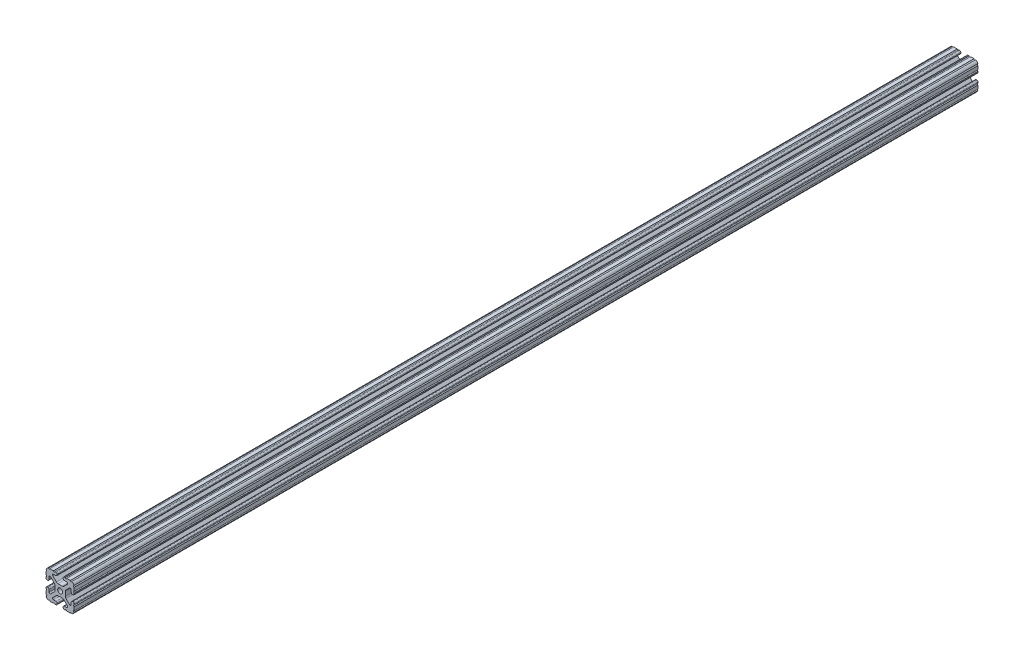
SolidWorks part; units mm, degrees
ref_plane "Front Plane" through (0, 0, 0) normal (0, 0, 1) x (1, 0, 0)
ref_plane "Top Plane" through (0, 0, 0) normal (0, 1, 0) x (1, 0, 0)
ref_plane "Right Plane" through (0, 0, 0) normal (1, 0, 0) x (0, 0, -1)
sketch "Sketch2" plane through (0, 0, 0) normal (0, 0, 1) x (1, 0, 0)
  line L0 (0, 19.05) -> (0, -19.05) construction
  line L1 (-19.05, 0) -> (19.05, 0) construction
  line L2 (4.064, -19.05) -> (19.05, -19.05)
  line L3 (19.05, -19.05) -> (19.05, -4.064)
  line L4 (4.064, -19.05) -> (4.064, -14.986)
  line L5 (4.064, -14.986) -> (12.1123, -14.986)
  line L6 (12.1123, -14.986) -> (4.1113, -6.985)
  line L7 (0, 0) -> (19.05, -19.05) construction
  line L8 (19.05, -4.064) -> (14.986, -4.064)
  line L9 (14.986, -4.064) -> (14.986, -12.1123)
  line L10 (14.986, -12.1123) -> (6.985, -4.1113)
  circle A0 centre (0, 0) radius 3.3274
  arc A1 (8.9963, -14.986) -> (9.909, -12.7826) centre (8.9963, -13.6953) ccw construction
  point P8 (0, -6.985)
  dimension "Center Hole Diameter" = 6.6548
  dimension "Rail Height" = 38.1
  dimension "Rail Width" = 38.1
  dimension "T-Slot Width" = 8.128
  dimension "Slot Inner Width" = 20.574
  dimension "Thickness" = 4.064
  dimension "Slot Depth" = 8.001
  dimension "D1" = 4.064
sketch "Sketch3" plane through (0, 0, 0) normal (1, 0, 0) x (0, 0, -1)
  line L0 (-609.6, -19.05) -> (609.6, -19.05) construction
  line L1 (-584.2, 0) -> (584.2, 0) construction
  dimension "Length" = 1219.2
  dimension "D1" = 25.4
sketch "Sketch4" plane through (0, 0, 0) normal (0, 0, 1) x (1, 0, 0)
  line L0 (5.7912, -19.05) -> (14.3002, -19.05)
  line L1 (4.064, -19.05) -> (19.05, -19.05) construction
  line L2 (4.064, -19.05) -> (4.064, -14.986) construction
  line L3 (4.064, -14.986) -> (12.1123, -14.986) construction
  line L4 (4.064, -16.7132) -> (4.064, -17.3228)
  line L5 (5.7912, -14.986) -> (8.9963, -14.986)
  line L6 (0, -6.985) -> (2.833, -6.985)
  line L7 (12.1123, -14.986) -> (4.1113, -6.985) construction
  line L8 (5.0152, -7.8889) -> (9.909, -12.7826)
  line L9 (19.05, -19.05) -> (19.05, -4.064) construction
  line L10 (14.986, -12.1123) -> (6.985, -4.1113) construction
  line L11 (14.986, -4.064) -> (14.986, -12.1123) construction
  line L12 (14.986, -8.9963) -> (14.986, -5.7912)
  line L13 (19.05, -4.064) -> (14.986, -4.064) construction
  line L14 (16.7132, -4.064) -> (17.3228, -4.064)
  line L15 (19.05, -5.7912) -> (19.05, -14.3002)
  line L16 (12.7826, -9.909) -> (7.8889, -5.0152)
  line L17 (6.985, 0) -> (6.985, -2.833)
  line L18 (-19.05, 0) -> (19.05, 0) construction
  line L19 (0, -6.985) -> (0, -3.3274)
  line L20 (0, 19.05) -> (0, -19.05) construction
  line L21 (6.985, 0) -> (3.3274, 0)
  arc A0 (4.064, -17.3228) -> (5.7912, -19.05) centre (5.7912, -17.3228) ccw
  arc A2 (4.064, -16.7132) -> (5.7912, -14.986) centre (5.7912, -16.7132) cw
  arc A3 (8.9963, -14.986) -> (9.909, -12.7826) centre (8.9963, -13.6953) ccw
  arc A4 (2.833, -6.985) -> (5.0152, -7.8889) centre (2.833, -10.0711) cw
  arc A5 (14.3002, -19.05) -> (19.05, -14.3002) centre (14.3002, -14.3002) ccw
  arc A6 (12.7826, -9.909) -> (14.986, -8.9963) centre (13.6953, -8.9963) ccw
  arc A7 (14.986, -5.7912) -> (16.7132, -4.064) centre (16.7132, -5.7912) cw
  arc A8 (17.3228, -4.064) -> (19.05, -5.7912) centre (17.3228, -5.7912) cw
  arc A9 (7.8889, -5.0152) -> (6.985, -2.833) centre (10.0711, -2.833) cw
  circle A10 centre (0, 0) radius 3.3274 construction
  arc A11 (0, -3.3274) -> (3.3274, 0) centre (0, 0) ccw
  dimension "D1" = 4.7498
  dimension "D2" = 3.0861
  dimension "D3" = 1.7272
extrude "Boss-Extrude1" add sketch "Sketch4" along normal mid plane 1219.2
sketch "Sketch5" plane through (0, 0, 0) normal (0, 0, 1) x (1, 0, 0)
  line L0 (4.064, -19.05) -> (19.05, -19.05) construction
  line L1 (5.7912, -14.986) -> (8.9963, -14.986) construction
  line L3 (0, 0) -> (19.05, -19.05) construction
  line L4 (8.9963, -14.986) -> (8.9963, -19.05) construction
  line L5 (12.1123, -14.986) -> (4.1113, -6.985) construction
  circle A0 centre (14.7395, -19.05) radius 1.016
  circle A1 centre (7.9803, -19.05) radius 1.016
  circle A2 centre (19.05, -14.7395) radius 1.016
  circle A3 centre (19.05, -7.9803) radius 1.016
  point P10 (7.3938, -14.986)
  point P12 (13.6953, -8.9963)
  dimension "D1" = 2.032
extrude "Cut-Extrude1" cut sketch "Sketch5" against normal through all both and the other way through all
mirror "Mirror1" about plane through (0, 0, 0) normal (1, 0, 0) of bodies 137 134
mirror "Mirror2" about plane through (0, 0, 0) normal (0, 1, 0) of bodies 135
equation "\"D1@Boss-Extrude1\"=\"Length@Sketch3\""
equation "\"D1@Sketch2\"=\"Thickness@Sketch2\""
equation "\"D2@Sketch4\"=\"Slot Inner Width@Sketch2\"*0.15"
equation "\"D1@Sketch4\"=\"D3@Sketch4\"*2.75"
equation "\"D3@Sketch4\"=\"Thickness@Sketch2\"*0.425"
equation "\"D1@Sketch5\"=\"Thickness@Sketch2\"*0.5"
